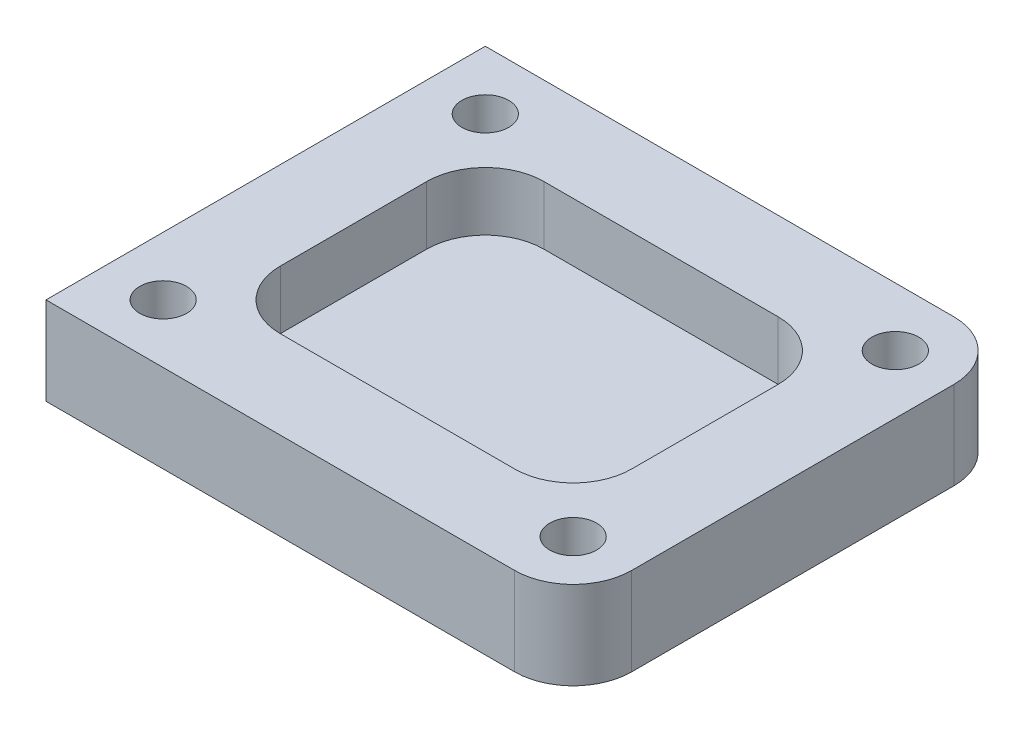
SolidWorks part; units mm, degrees
ref_plane "Front Plane" through (0, 0, 0) normal (0, 0, 1) x (1, 0, 0)
ref_plane "Top Plane" through (0, 0, 0) normal (0, 1, 0) x (1, 0, 0)
ref_plane "Right Plane" through (0, 0, 0) normal (1, 0, 0) x (0, 0, -1)
sketch "Sketch1" plane through (0, 0, 0) normal (0, 1, 0) x (1, 0, 0)
  line L1 (-90, -75) -> (90, -75)
  line L2 (-90, -75) -> (-90, 75)
  line L3 (-90, 75) -> (90, 75)
  line L4 (90, -75) -> (90, 75)
  line L5 (-90, -75) -> (90, 75) construction
  line L6 (-90, 75) -> (90, -75) construction
  point P0 (0, 0)
  dimension "D1" = 180
  dimension "D2" = 150
extrude "Boss-Extrude1" add sketch "Sketch1" along normal blind 30
sketch "Sketch2" plane through (0, 30, 0) normal (0, 1, 0) x (1, 0, 0)
  line L8 (70, -55) -> (70, 55)
  line L9 (70, 55) -> (-70, 55)
  line L10 (-70, 55) -> (-70, -55)
  line L11 (-70, -55) -> (70, -55)
  line L12 (70, -55) -> (70, 55) construction
  line L13 (70, 55) -> (-70, 55) construction
  line L14 (-70, 55) -> (-70, -55) construction
  line L15 (-70, -55) -> (70, -55) construction
  dimension "D1" = 20
hole_wizard "Ø16.0mm Dowel Hole1" positions "3DSketch2" profile "Sketch4" hole size "Ø16.0" standard "ANSI Metric"
sketch3d "3DSketch2"
  point P0 (-70, 30, 55)
  point P3 (-70, 30, -55)
  point P6 (70, 30, -55)
  point P9 (70, 30, 55)
sketch "Sketch4" plane through (-70, 30, 55) normal (1, 0, 0) x (0, 0, 1)
  line L0 (0, 0) -> (0, 19.8069)
  line L1 (0, 19.8069) -> (8, 15)
  line L2 (8, 15) -> (8, 0)
  line L5 (8, 0) -> (0, 0)
  line L10 (0, 19.8069) -> (-8, 15) construction
  line L11 (0, -6.35) -> (0, 107.95) construction
  dimension "Hole Dia." = 16
  dimension "Hole Depth" = 15
  dimension "Drill Angle" = 118
sketch "Sketch5" plane through (0, 30, 0) normal (0, 1, 0) x (1, 0, 0)
  line L8 (60, -45) -> (60, 45)
  line L9 (60, 45) -> (-60, 45)
  line L10 (-60, 45) -> (-60, -45)
  line L11 (-60, -45) -> (60, -45)
  line L12 (60, -45) -> (60, 45)
  line L13 (60, 45) -> (-60, 45)
  line L14 (-60, 45) -> (-60, -45)
  line L15 (-60, -45) -> (60, -45)
  dimension "D1" = 30
extrude "Cut-Extrude1" cut sketch "Sketch5" against normal offset from surface (20 mm away) 10 up to face at (0, 0, 0)
fillet "Fillet1" radius 20 4 edges at (60, 20, 45) (-60, 20, 45) (60, 20, -45) (-60, 20, -45)
fillet "Fillet2" radius 20 2 edges at (90, 15, 75) (90, 15, -75)
